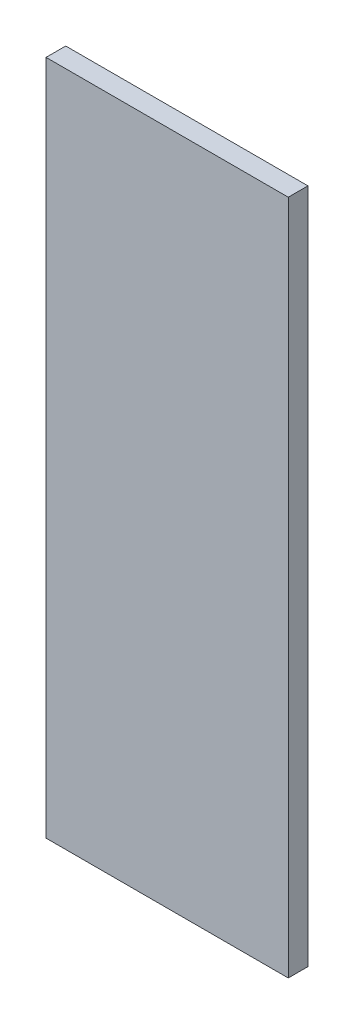
SolidWorks part; units mm, degrees
ref_plane "Front Plane" through (0, 0, 0) normal (0, 0, 1) x (1, 0, 0)
ref_plane "Top Plane" through (0, 0, 0) normal (0, 1, 0) x (1, 0, 0)
ref_plane "Right Plane" through (0, 0, 0) normal (1, 0, 0) x (0, 0, -1)
sketch "Sketch1" plane through (0, 0, 0) normal (0, 0, 1) x (1, 0, 0)
  line L1 (-98.5, 275) -> (98.5, 275)
  line L2 (-98.5, 275) -> (-98.5, -275)
  line L3 (-98.5, -275) -> (98.5, -275)
  line L4 (98.5, 275) -> (98.5, -275)
  point P4 (98.5, 0)
  point P5 (0, -275)
  dimension "D1" = 550
  dimension "D2" = 197
extrude "Boss-Extrude1" add sketch "Sketch1" along normal blind 16 contours L2 L3 L4 L1
equation "\"Length\"= 45cm"
equation "\"Width\" = 16cm"
equation "\"Curvature radius\"= 13mm"
equation "\"Extra\"= 5cm"
equation "\"D1@Sketch1\"=\"Length\"+\"Extra\"*2"
equation "\"D2@Sketch1\" = \"Width\" + \"Extra\" - \"Curvature radius\""
